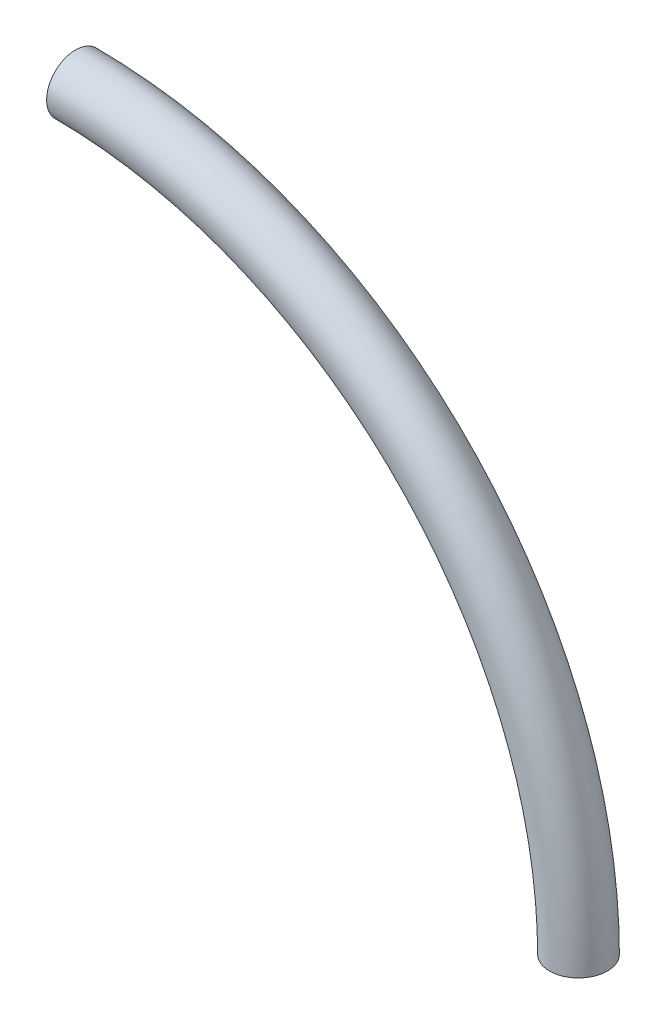
SolidWorks part; units mm, degrees
ref_plane "Alzado" through (0, 0, 0) normal (0, 0, 1) x (1, 0, 0)
ref_plane "Planta" through (0, 0, 0) normal (0, 1, 0) x (1, 0, 0)
ref_plane "Vista lateral" through (0, 0, 0) normal (1, 0, 0) x (0, 0, -1)
sketch "Croquis5" plane through (0, 0, 0) normal (0, 0, 1) x (1, 0, 0)
  line L0 (0, 0) -> (0, 200) construction
  line L1 (0, 0) -> (200, 0) construction
  arc A0 (0, 200) -> (200, 0) centre (0, 0) cw
  dimension "D1" = 200
  dimension "D2" = 200
sketch "Croquis6" plane through (0, 0, 0) normal (0, 1, 0) x (1, 0, 0)
  circle A0 centre (200, 0) radius 8.5
  circle A1 centre (200, 0) radius 11.5
  dimension "D1" = 17
  dimension "D2" = 3
sweep "Barrer2" add profiles "Croquis6" path "Croquis5"
